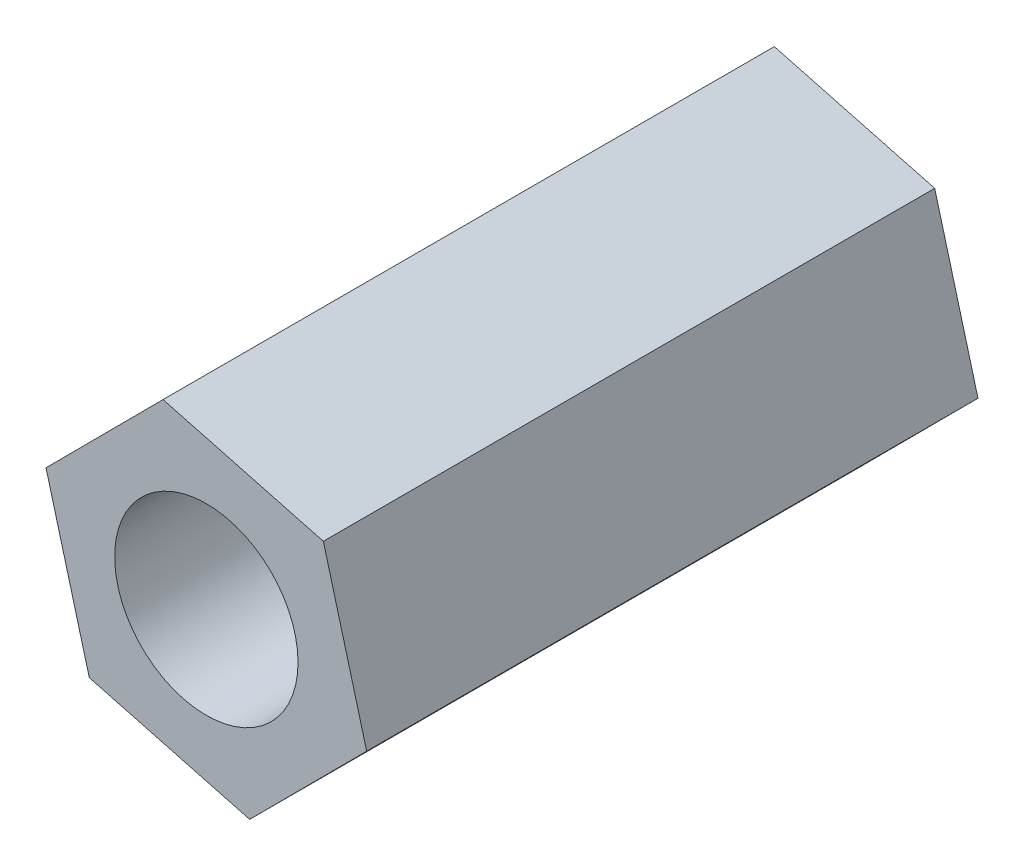
SolidWorks part; units mm, degrees
ref_plane "Front Plane" through (0, 0, 0) normal (0, 0, 1) x (1, 0, 0)
ref_plane "Top Plane" through (0, 0, 0) normal (0, 1, 0) x (1, 0, 0)
ref_plane "Right Plane" through (0, 0, 0) normal (1, 0, 0) x (0, 0, -1)
sketch "Sketch1" plane through (0, 0, 0) normal (0, 0, 1) x (1, 0, 0)
  line L1 (1.9142, 1.9233) -> (-0.7085, 2.6194)
  line L2 (-0.7085, 2.6194) -> (-2.6227, 0.6961)
  line L3 (-2.6227, 0.6961) -> (-1.9142, -1.9233)
  line L4 (-1.9142, -1.9233) -> (0.7085, -2.6194)
  line L5 (0.7085, -2.6194) -> (2.6227, -0.6961)
  line L6 (2.6227, -0.6961) -> (1.9142, 1.9233)
  circle A0 centre (0, 0) radius 2.35 construction
  circle A1 centre (0, 0) radius 1.5
  dimension "D2" = 3
  dimension "D1" = 4.7
extrude "Boss-Extrude1" add sketch "Sketch1" along normal blind 10
